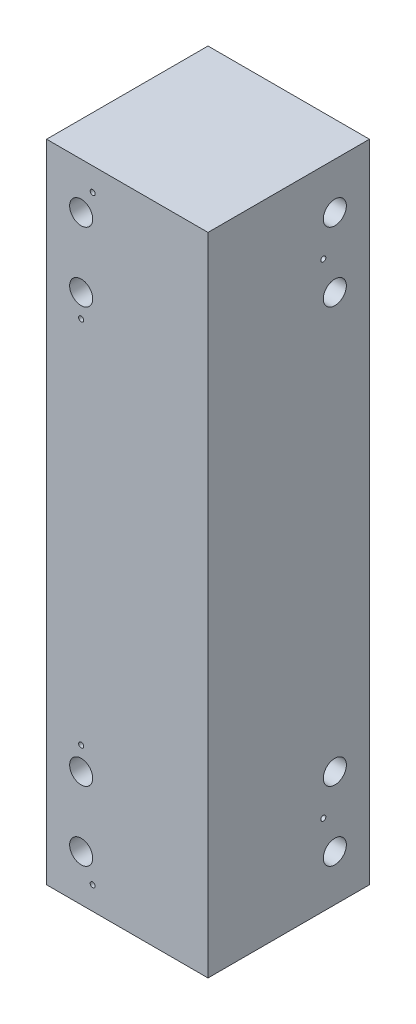
SolidWorks part; units mm, degrees
ref_plane "Front Plane" through (0, 0, 0) normal (0, 0, 1) x (1, 0, 0)
ref_plane "Top Plane" through (0, 0, 0) normal (0, 1, 0) x (1, 0, 0)
ref_plane "Right Plane" through (0, 0, 0) normal (1, 0, 0) x (0, 0, -1)
sketch "Sketch1" plane through (0, 0, 0) normal (0, 1, 0) x (1, 0, 0)
  line L1 (0, 0) -> (88.9, 0)
  line L2 (0, 0) -> (0, -88.9)
  line L3 (0, -88.9) -> (88.9, -88.9)
  line L4 (88.9, 0) -> (88.9, -88.9)
  dimension "D1" = 88.9
  dimension "D2" = 88.9
extrude "Boss-Extrude1" add sketch "Sketch1" along normal blind 355.6
sketch "Sketch2" plane through (0, 0, 88.9) normal (0, 0, 1) x (1, 0, 0)
  line L0 (19.05, 0) -> (19.05, 355.6) construction
  line L3 (0, 355.6) -> (0, 0) construction
  line L4 (0, 355.6) -> (88.9, 355.6) construction
  line L5 (0, 0) -> (88.9, 0) construction
  circle A0 centre (19.05, 342.9) radius 1.3891 construction
  circle A1 centre (19.05, 12.7) radius 1.3891 construction
  circle A2 centre (19.05, 76.2) radius 1.3891
  circle A3 centre (19.05, 279.4) radius 1.3891
  circle A4 centre (25.4, 342.9) radius 1.3891
  circle A5 centre (25.4, 12.7) radius 1.3891
  dimension "D1" = 2.7781
  dimension "D2" = 12.7
  dimension "D3" = 12.7
  dimension "D4" = 19.05
  dimension "D5" = 76.2
  dimension "D6" = 76.2
  dimension "D7" = 25.4
  dimension "D8" = 25.4
extrude "Cut-Extrude1" cut sketch "Sketch2" against normal through all both
sketch "Sketch3" plane through (0, 0, 0) normal (-1, 0, 0) x (0, 0, 1)
  line L0 (25.4, 355.6) -> (25.4, 0) construction
  line L1 (0, 0) -> (88.9, 0) construction
  line L3 (0, 355.6) -> (88.9, 355.6) construction
  line L4 (0, 355.6) -> (0, 0) construction
  circle A0 centre (25.4, 311.15) radius 1.3891
  circle A1 centre (25.4, 44.45) radius 1.3891
  dimension "D1" = 2.7781
  dimension "D2" = 44.45
  dimension "D3" = 44.45
  dimension "D5" = 25.4
extrude "Cut-Extrude2" cut sketch "Sketch3" against normal through all both
sketch "Sketch4" plane through (0, 0, 88.9) normal (0, 0, 1) x (1, 0, 0)
  line L0 (19.05, 330.2) -> (19.05, 292.1) construction
  line L1 (19.05, 63.5) -> (19.05, 25.4) construction
  line L2 (19.05, 0) -> (19.05, 25.4) construction
  line L3 (0, 0) -> (88.9, 0) construction
  line L4 (19.05, 330.2) -> (19.05, 355.6) construction
  line L5 (0, 355.6) -> (88.9, 355.6) construction
  line L6 (88.9, 25.4) -> (19.05, 25.4) construction
  line L7 (88.9, 355.6) -> (88.9, 0) construction
  line L8 (88.9, 292.1) -> (19.05, 292.1) construction
  line L9 (25.4, 12.7) -> (25.4, 76.2) construction
  line L10 (25.4, 76.2) -> (19.05, 76.2) construction
  line L11 (0, 355.6) -> (0, 0) construction
  circle A0 centre (19.05, 330.2) radius 6.35
  circle A1 centre (19.05, 292.1) radius 6.35
  circle A2 centre (19.05, 63.5) radius 6.35
  circle A3 centre (19.05, 25.4) radius 6.35
  point P18 (25.4, 44.45)
  point P20 (19.05, 44.45)
  dimension "D1" = 12.7
  dimension "D2" = 38.1
  dimension "D3" = 19.05
sketch "Sketch5" plane through (88.9, 0, 0) normal (-1, 0, 0) x (0, 0, 1)
  line L0 (19.05, 330.2) -> (19.05, 292.1) construction
  line L1 (19.05, 63.5) -> (19.05, 25.4) construction
  line L2 (19.05, 0) -> (19.05, 25.4) construction
  line L3 (19.05, 330.2) -> (19.05, 355.6) construction
  line L4 (88.9, 25.4) -> (19.05, 25.4) construction
  line L5 (88.9, 292.1) -> (19.05, 292.1) construction
  line L8 (0, 0) -> (88.9, 0) construction
  line L9 (88.9, 355.6) -> (88.9, 0) construction
  line L10 (0, 355.6) -> (88.9, 355.6) construction
  line L11 (0, 355.6) -> (0, 0) construction
  circle A0 centre (19.05, 330.2) radius 6.35
  circle A1 centre (19.05, 292.1) radius 6.35
  circle A2 centre (19.05, 63.5) radius 6.35
  circle A3 centre (19.05, 25.4) radius 6.35
  point P11 (25.4, 44.45)
  point P16 (19.05, 44.45)
  dimension "D1" = 12.7
  dimension "D2" = 38.1
  dimension "D3" = 19.05
hole_wizard "1/2 (0.5) Diameter Hole1" positions "3DSketch1" profile "Sketch6" hole size "1/2" standard "ANSI Inch"
sketch3d "3DSketch1"
  point P0 (19.05, 292.1, 88.9)
  point P3 (19.05, 330.2, 88.9)
  point P6 (19.05, 25.4, 88.9)
  point P9 (19.05, 63.5, 88.9)
  point P12 (88.9, 63.5, 19.05)
  point P15 (88.9, 25.4, 19.05)
  point P18 (88.9, 330.2, 19.05)
  point P21 (88.9, 292.1, 19.05)
sketch "Sketch6" plane through (19.05, 292.1, 88.9) normal (1, 0, 0) x (0, -1, 0)
  line L0 (0, 0) -> (0, 22.8655)
  line L1 (0, 22.8655) -> (6.35, 19.05)
  line L2 (6.35, 19.05) -> (6.35, 0)
  line L5 (6.35, 0) -> (0, 0)
  line L10 (0, 22.8655) -> (-6.35, 19.05) construction
  line L11 (0, -6.35) -> (0, 107.95) construction
  dimension "Hole Dia." = 12.7
  dimension "Hole Depth" = 19.05
  dimension "Drill Angle" = 118
sketch "Sketch8" plane through (0, 0, 0) normal (0, -1, 0) x (1, 0, 0)
  line L0 (12.7, 63.5) -> (12.7, 12.7) construction
  line L1 (12.7, 12.7) -> (63.5, 12.7) construction
  line L2 (63.5, 12.7) -> (63.5, 63.5) construction
  line L3 (63.5, 63.5) -> (12.7, 63.5) construction
  line L7 (88.9, 0) -> (0, 0) construction
  line L8 (0, 0) -> (0, 88.9) construction
  point P0 (12.7, 63.5)
  point P1 (63.5, 63.5)
  point P2 (63.5, 12.7)
  point P3 (12.7, 12.7)
  dimension "D1" = 12.7
  dimension "D2" = 12.7
  dimension "D3" = 63.5
  dimension "D4" = 63.5
hole_wizard "#10 (0.1935) Diameter Hole1" positions "3DSketch2" profile "Sketch9" hole size "#10" standard "ANSI Inch"
sketch3d "3DSketch2"
  point P0 (12.7, 0, 63.5)
  point P3 (63.5, 0, 63.5)
  point P6 (63.5, 0, 12.7)
  point P9 (12.7, 0, 12.7)
sketch "Sketch9" plane through (12.7, 0, 63.5) normal (1, 0, 0) x (0, 0, -1)
  line L0 (0, 0) -> (0, 52.2766)
  line L1 (0, 52.2766) -> (2.4574, 50.8)
  line L2 (2.4574, 50.8) -> (2.4574, 0)
  line L5 (2.4574, 0) -> (0, 0)
  line L10 (0, 52.2766) -> (-2.4575, 50.8) construction
  line L11 (0, -6.35) -> (0, 107.95) construction
  dimension "Hole Dia." = 4.9149
  dimension "Hole Depth" = 50.8
  dimension "Drill Angle" = 118
